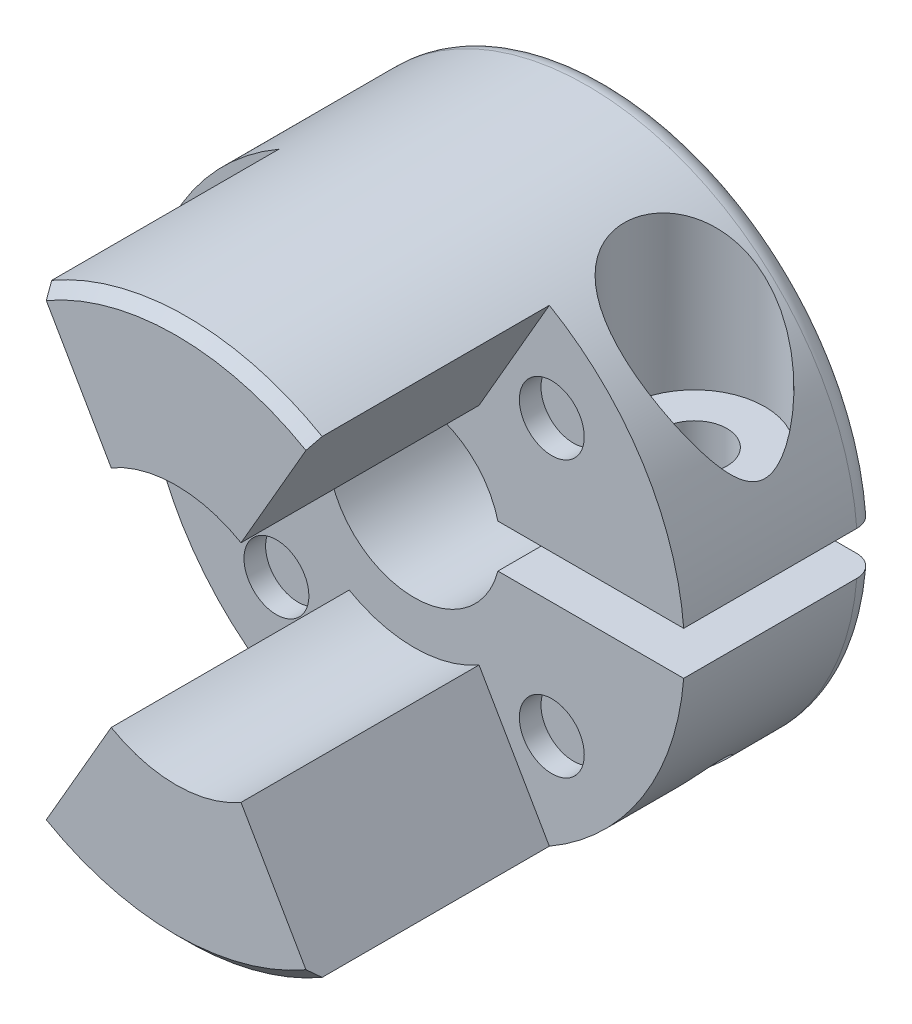
SolidWorks part; units mm, degrees
material "Liga 6061"
ref_plane "Plano frontal" through (0, 0, 0) normal (0, 0, 1) x (1, 0, 0)
ref_plane "Plano superior" through (0, 0, 0) normal (0, 1, 0) x (1, 0, 0)
ref_plane "Plano direito" through (0, 0, 0) normal (1, 0, 0) x (0, 0, -1)
sketch "Esboço1" plane through (0, 0, 0) normal (0, 0, 1) x (1, 0, 0)
  circle A0 centre (0, 0) radius 12.5
  dimension "D1" = 25
extrude "Ressalto-extrusão1" add sketch "Esboço1" along normal blind 20
sketch "Esboço2" plane through (0, 0, 20) normal (0, 0, 1) x (1, 0, 0)
  line L0 (0, 0) -> (0, 12.5) construction
  line L1 (0, 0) -> (6.25, 10.8253)
  line L2 (6.25, -10.8253) -> (0, 0)
  circle A0 centre (0, 0) radius 12.5 construction
  arc A2 (6.25, 10.8253) -> (6.25, -10.8253) centre (0, 0) cw
  dimension "D1" = 120
  dimension "D2" = 30
extrude "Corte-extrusão3" cut sketch "Esboço2" against normal blind 11
sketch "Esboço3" plane through (0, 0, 0) normal (0, 0, -1) x (-1, 0, 0)
  circle A0 centre (0, 0) radius 4
  dimension "D1" = 8
extrude "Corte-extrusão4" cut sketch "Esboço3" against normal through all
mirror "Espelhar1" about plane through (0, 0, 0) normal (1, 0, 0) of "Corte-extrusão3"
sketch "Esboço6" plane through (0, 0, 9) normal (0, 0, 1) x (1, 0, 0)
  line L1 (1, 1) -> (13, 1)
  line L2 (1, 1) -> (1, -1)
  line L3 (1, -1) -> (13, -1)
  line L4 (13, 1) -> (13, -1)
  line L5 (1, 1) -> (13, -1) construction
  line L6 (1, -1) -> (13, 1) construction
  point P0 (7, 0)
  dimension "D1" = 2
  dimension "D2" = 12
  dimension "D3" = 7
extrude "Corte-extrusão5" cut sketch "Esboço6" against normal through all
sketch "Esboço7" plane through (0, 1, 0) normal (0, -1, 0) x (1, 0, 0)
  line L0 (12.4599, 9) -> (12.4599, 0) construction
  circle A0 centre (8.4599, 4.5) radius 3.25
  point P4 (12.4599, 4.5)
  dimension "D1" = 6.5
  dimension "D2" = 4
extrude "Corte-extrusão6" cut sketch "Esboço7" against normal through all from offset 3 offset against normal yes
hole_wizard "Furo roscado de M3x0.51" positions "Esboço9" profile "Esboço8" tap size "M3x0.5" standard "Ansi Metric" end condition through all
sketch "Esboço9" plane through (0, 4, 0) normal (0, 1, 0) x (1, 0, 0)
  point P0 (8.4599, -4.5)
sketch "Esboço8" plane through (8.4599, 4, 4.5) normal (1, 0, 0) x (0, 0, 1)
  line L0 (0, 0) -> (0, 16.5)
  line L1 (0, 16.5) -> (1.25, 16.5)
  line L2 (1.25, 16.5) -> (1.25, 0)
  line L5 (1.25, 0) -> (0, 0)
  line L11 (0, -6.35) -> (0, 107.95) construction
  dimension "Thru Tap Drill Dia." = 2.5
  dimension "Thru Tap Drill Depth" = 16.5
cosmetic thread "Rosca de furo3" parameters "D2"=3
fillet "Filete1" radius 1 1 edges at (-12.5, 0, 0)
sketch "Esboço10" plane through (0, 0, 9) normal (0, 0, 1) x (1, 0, 0)
  line L0 (0, 0) -> (0, -3.9553) construction
  line L1 (6.364, -6.364) -> (0, 0) construction
  circle A0 centre (6.364, -6.364) radius 1.5
  dimension "D1" = 3
  dimension "D2" = 9
  dimension "D3" = 45
extrude "Corte-extrusão7" cut sketch "Esboço10" against normal blind 1
chamfer "Chanfro1" distance 0.5 angle 45 2 edges at (0, 12.5, 20) (0, -12.5, 20)
sketch "Esboço11" plane through (0, 4, 0) normal (0, 1, 0) x (1, 0, 0)
  circle A0 centre (8.4599, -4.5) radius 1.5
  dimension "D1" = 3
extrude "Corte-extrusão8" cut sketch "Esboço11" against normal up to next
sketch "Esboço12" plane through (0, 0, 20) normal (0, 0, 1) x (1, 0, 0)
  circle A0 centre (0, 0) radius 6
  dimension "D1" = 12
extrude "Corte-extrusão9" cut sketch "Esboço12" against normal up to surface (11 mm away) up to face at (6.5106, 4.3109, 9)
pattern_circular "PadrãoCircular1" count 4 over 360 about axis through (0, 0, 0) along (0, 0, 1) of "Corte-extrusão7"
chamfer "Chanfro2" distance 0.5 angle 45 1 edges at (-4, 0, 0)
